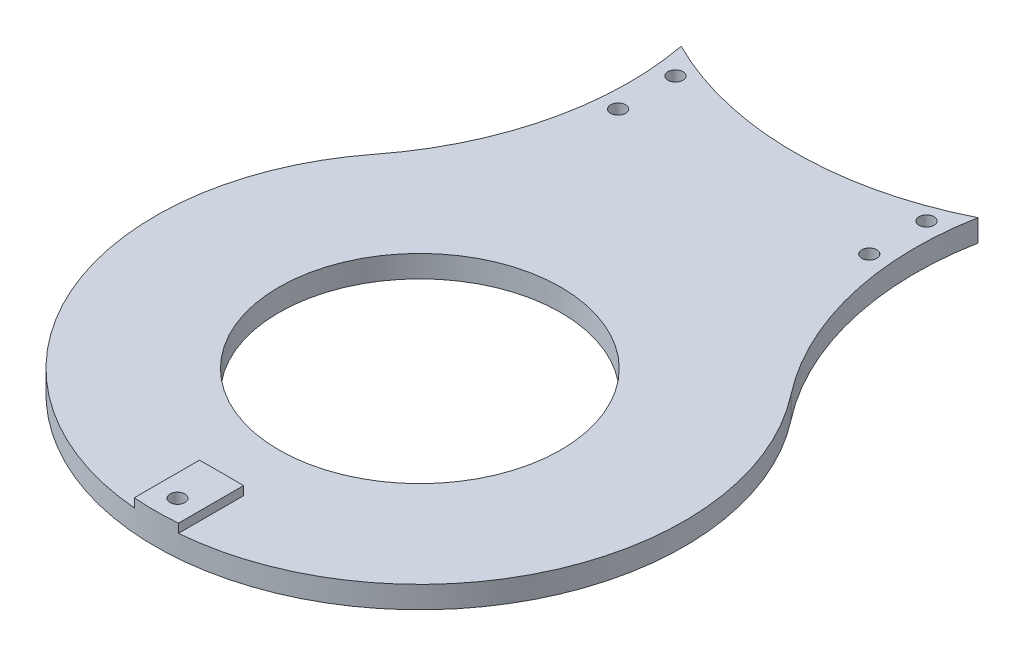
SolidWorks part; units mm, degrees
material "PLA"
ref_plane "Alzado" through (0, 0, 0) normal (0, 0, 1) x (1, 0, 0)
ref_plane "Planta" through (0, 0, 0) normal (0, 1, 0) x (1, 0, 0)
ref_plane "Vista lateral" through (0, 0, 0) normal (1, 0, 0) x (0, 0, -1)
sketch "Croquis1" plane through (0, 0, 0) normal (0, 1, 0) x (1, 0, 0)
  circle A0 centre (0, 0) radius 32
  arc A1 (-47.2936, 36.9231) -> (47.2936, 36.9231) centre (0, 0) ccw
  circle A2 centre (0, 160) radius 32
  arc A3 (47.2936, 123.0769) -> (-47.2936, 123.0769) centre (0, 160) ccw
  arc A4 (47.2936, 123.0769) -> (47.2936, 36.9231) centre (102.4695, 80) ccw
  arc A5 (-47.2936, 36.9231) -> (-47.2936, 123.0769) centre (-102.4695, 80) ccw
  dimension "D2" = 120
  dimension "D3" = 140
  dimension "D4" = 64
  dimension "D1" = 160
extrude "Saliente-Extruir1" add sketch "Croquis1" along normal blind 5
sketch "Croquis2" plane through (0, 5, 0) normal (0, 1, 0) x (1, 0, 0)
  line L1 (5, 205) -> (-5, 205)
  line L2 (5, 205) -> (5, 219.7913)
  line L4 (-5, 205) -> (-5, 219.7913)
  line L7 (-5, -45) -> (5, -45)
  line L8 (-5, -45) -> (-5, -59.7913)
  line L10 (5, -45) -> (5, -59.7913)
  circle A0 centre (0, 160) radius 32 construction
  arc A1 (-47.2936, 36.9231) -> (47.2936, 36.9231) centre (0, 0) ccw construction
  arc A2 (47.2936, 123.0769) -> (-47.2936, 123.0769) centre (0, 160) ccw construction
  arc A3 (-5, -59.7913) -> (5, -59.7913) centre (0, 0) ccw
  arc A4 (5, 219.7913) -> (-5, 219.7913) centre (0, 160) ccw
  point P0 (0, 205)
  point P6 (0, -45)
  dimension "D1" = 45
  dimension "D2" = 45
  dimension "D3" = 10
  dimension "D4" = 10
extrude "Saliente-Extruir2" add sketch "Croquis2" along normal blind 2
sketch "Croquis3" plane through (0, 7, 0) normal (0, 1, 0) x (1, 0, 0)
  circle A0 centre (0, 215) radius 1.7
  circle A1 centre (0, -55) radius 1.7
  circle A2 centre (0, 160) radius 32 construction
  dimension "D3" = 3.4
  dimension "D1" = 55
  dimension "D2" = 55
extrude "Cortar-Extruir1" cut sketch "Croquis3" against normal blind 19
sketch "Croquis4" plane through (0, 0, 0) normal (0, -1, 0) x (1, 0, 0)
  circle A0 centre (0, 55) radius 2.95
  circle A1 centre (0, -215) radius 2.95
  dimension "D1" = 5.9
extrude "Cortar-Extruir2" cut sketch "Croquis4" against normal blind 3
sketch "Croquis5" plane through (0, 0, 0) normal (0, -1, 0) x (1, 0, 0)
  line L0 (0, 0) -> (0, -160) construction
  line L1 (28.5, -86.5) -> (-28.5, -86.5) construction
  line L2 (28.5, -86.5) -> (28.5, -73.5) construction
  line L3 (28.5, -73.5) -> (-28.5, -73.5) construction
  line L4 (-28.5, -86.5) -> (-28.5, -73.5) construction
  line L5 (28.5, -86.5) -> (-28.5, -73.5) construction
  line L6 (28.5, -73.5) -> (-28.5, -86.5) construction
  circle A0 centre (-28.5, -73.5) radius 1.7
  circle A1 centre (-28.5, -86.5) radius 1.7
  circle A2 centre (28.5, -86.5) radius 1.7
  circle A3 centre (28.5, -73.5) radius 1.7
  point P0 (0, -80)
  point P10 (0, -80)
  dimension "D1" = 3.4
  dimension "D2" = 13
  dimension "D3" = 57
extrude "Cortar-Extruir3" cut sketch "Croquis5" against normal blind 5
sketch "Croquis9" plane through (0, 0, 0) normal (0, -1, 0) x (1, 0, 0)
  circle A0 centre (0, -160) radius 75
  dimension "D1" = 150
extrude "Cortar-Extruir6" cut sketch "Croquis9" against normal blind 37
